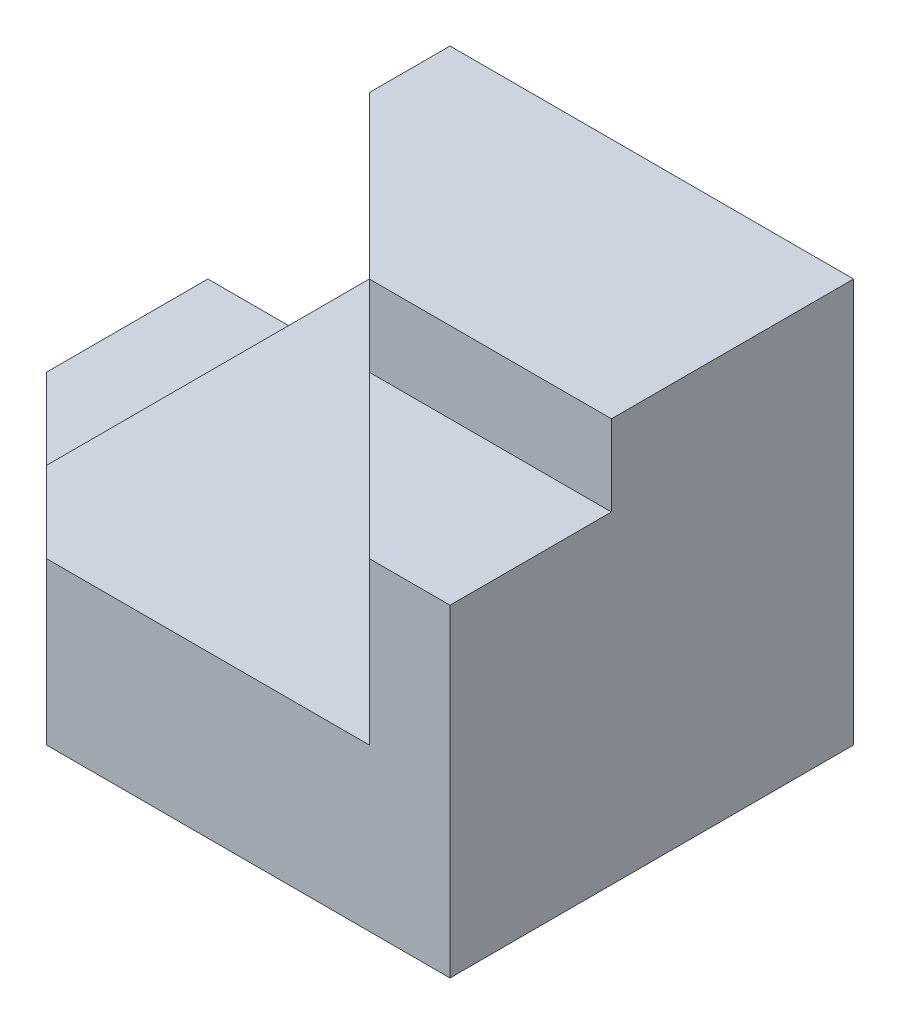
SolidWorks part; units mm, degrees
ref_plane "Front Plane" through (0, 0, 0) normal (0, 0, 1) x (1, 0, 0)
ref_plane "Top Plane" through (0, 0, 0) normal (0, 1, 0) x (1, 0, 0)
ref_plane "Right Plane" through (0, 0, 0) normal (1, 0, 0) x (0, 0, -1)
sketch "Sketch1" plane through (0, 0, 0) normal (0, 1, 0) x (1, 0, 0)
  line L1 (0, 0) -> (80, 0)
  line L2 (0, 0) -> (0, 50)
  line L3 (0, 50) -> (80, 50)
  line L4 (80, 0) -> (80, 50)
  dimension "D1" = 80
  dimension "D2" = 50
extrude "Boss-Extrude1" add sketch "Sketch1" along normal blind 10
sketch "Sketch2" plane through (0, 10, 0) normal (0, 1, 0) x (1, 0, 0)
  line L0 (0, 30) -> (30, 0)
  line L1 (0, 50) -> (0, 0) construction
  line L2 (0, 0) -> (80, 0) construction
  line L3 (30, 0) -> (0, 0)
  line L4 (0, 0) -> (0, 30)
  dimension "D1" = 30
  dimension "D2" = 30
extrude "Cut-Extrude1" cut sketch "Sketch2" against normal blind 10
sketch "Sketch3" plane through (0, 10, 0) normal (0, 1, 0) x (1, 0, 0)
  line L0 (80, 50) -> (80, 0)
  line L1 (80, 0) -> (30, 0)
  line L2 (30, 0) -> (20, 10)
  line L3 (30, 0) -> (0, 30) construction
  line L4 (20, 10) -> (20, 50)
  line L5 (80, 50) -> (0, 50) construction
  line L6 (20, 50) -> (80, 50)
  dimension "D1" = 20
extrude "Boss-Extrude2" add sketch "Sketch3" along normal blind 10
sketch "Sketch4" plane through (0, 20, 0) normal (0, 1, 0) x (1, 0, 0)
  line L0 (80, 50) -> (80, 0)
  line L1 (80, 0) -> (70, 0)
  line L2 (30, 0) -> (80, 0) construction
  line L3 (70, 0) -> (30, 40)
  line L4 (30, 40) -> (30, 50)
  line L5 (80, 50) -> (20, 50) construction
  line L6 (30, 50) -> (80, 50)
  dimension "D1" = 10
  dimension "D2" = 10
  dimension "D3" = 50
extrude "Boss-Extrude3" add sketch "Sketch4" along normal blind 20
sketch "Sketch5" plane through (0, 40, 0) normal (0, 1, 0) x (1, 0, 0)
  line L0 (80, 50) -> (80, 20)
  line L1 (80, 0) -> (80, 50) construction
  line L2 (80, 20) -> (50, 20)
  line L3 (30, 40) -> (70, 0) construction
  line L4 (50, 20) -> (30, 40)
  line L5 (30, 40) -> (30, 50)
  line L6 (30, 50) -> (80, 50)
  dimension "D1" = 30
extrude "Boss-Extrude4" add sketch "Sketch5" along normal blind 10
